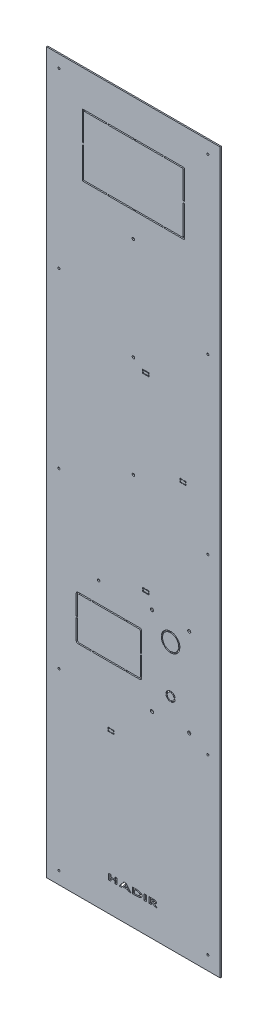
SolidWorks part; units mm, degrees
ref_plane "Front Plane" through (0, 0, 0) normal (0, 0, 1) x (1, 0, 0)
ref_plane "Top Plane" through (0, 0, 0) normal (0, 1, 0) x (1, 0, 0)
ref_plane "Right Plane" through (0, 0, 0) normal (1, 0, 0) x (0, 0, -1)
sketch "Sketch2" plane through (0, 0, 0) normal (0, 0, 1) x (1, 0, 0)
  line L0 (140, 680) -> (100, 680) construction
  line L5 (0, -480) -> (0, 680) construction
  line L6 (-140, 0) -> (140, 0) construction
  line L7 (100, 680) -> (100, 750.5127) construction
  line L8 (100, 750.5127) -> (100, -538.4561) construction
  line L9 (-140, 680) -> (-100, 680) construction
  line L10 (-100, 680) -> (-100, 750.5127) construction
  line L11 (-100, 750.5127) -> (-100, -538.4561) construction
  line L12 (-140, 680) -> (-140, 150) construction
  line L14 (-140, 680) -> (140, 680)
  line L15 (140, 680) -> (140, 580)
  line L17 (-140, -480) -> (140, -480)
  line L19 (140, -480) -> (140, 580)
  line L20 (-140, -480) -> (-140, 680)
  line L21 (-140, 150) -> (140, 150) construction
  line L22 (140, 150) -> (140, 110) construction
  line L23 (140, 110) -> (-140, 110) construction
  line L24 (0, 680) -> (0, 640) construction
  line L25 (-197.3636, 640) -> (197.5047, 640) construction
  line L26 (0, -480) -> (0, -440) construction
  line L27 (197.5047, -440) -> (-197.3636, -440) construction
  point P0 (0, 0)
  dimension "D1" = 1160
extrude "Boss-Extrude2" add sketch "Sketch2" along normal blind 2
sketch "Sketch3" plane through (0, 0, 0) normal (0, 0, 1) x (1, 0, 0)
  line L0 (120, 660) -> (120, 380.6) construction
  line L2 (-140, 660) -> (-120, 660) construction
  line L3 (120, 380.6) -> (-120, 380.6) construction
  line L4 (-120, 660) -> (-120, 680) construction
  line L5 (120, -457.6) -> (120, 101.2) construction
  line L6 (120, 101.2) -> (-120, 101.2) construction
  line L7 (-120, 680) -> (-120, 150) construction
  line L8 (-198.9172, 110) -> (186.996, 110) construction
  line L9 (-140, -480) -> (-100, -480) construction
  line L10 (60, -163) -> (90, -163) construction
  line L11 (0, 481.6) -> (0, 316.5) construction
  line L12 (-198.9172, 150) -> (186.996, 150) construction
  line L13 (0, 316.5) -> (0, 304.5) construction
  line L14 (186.996, 150) -> (186.996, 110) construction
  line L16 (60, -163) -> (30, -163) construction
  line L17 (-56.1, -21) -> (-56.1, -23) construction
  line L20 (-140, 680) -> (140, 680) construction
  line L23 (140, 660) -> (120, 660) construction
  line L24 (-56.1, 150) -> (-56.1, 110) construction
  line L25 (60, -21) -> (60, -36) construction
  line L26 (60, 0) -> (60, -21) construction
  line L27 (60, -21) -> (90, -21) construction
  line L28 (60, -127) -> (60, -163) construction
  line L29 (90, -163) -> (90, -21) construction
  line L30 (30, -163) -> (30, -21) construction
  line L31 (30, -21) -> (60, -21) construction
  line L127 (-140, 680) -> (-140, 640) construction
  line L132 (60, -36) -> (60, -38)
  line L137 (59.0006, -36.0333) -> (59.1224, -38.0297)
  line L222 (59.958, -51.042) -> (70.6066, -40.3934) construction
  line L223 (59.958, -51.042) -> (70.5575, -61.6415) construction
  line L224 (60, -51) -> (50.8076, -41.8076) construction
  line L225 (59.958, -51.042) -> (49.3934, -61.6066) construction
  line L230 (74.9337, -52.4092) -> (72.9425, -52.2213)
  line L231 (74.8066, -53.4011) -> (72.8324, -53.0809)
  line L232 (60, -66) -> (60, -64)
  line L233 (59.0005, -65.9671) -> (59.0005, -63.9615)
  line L250 (67.5, -127) -> (52.5, -127) construction
  line L251 (60, -127) -> (60, -119.5) construction
  line L252 (60, -119.5) -> (60, -121.5) construction
  line L253 (67.5, -127) -> (65.5, -127) construction
  line L254 (65.5, -127) -> (60, -127) construction
  line L255 (60, -127) -> (60, -132.5) construction
  line L256 (60, -127) -> (54.6967, -121.6967) construction
  line L257 (60, -127) -> (65.3033, -132.3033) construction
  line L258 (60, -127) -> (54.6967, -132.3033) construction
  line L259 (60, -127) -> (65.3033, -121.6967) construction
  line L260 (60.9806, -119.5644) -> (60.7191, -121.5472)
  line L261 (67.4356, -126.0194) -> (65.4528, -126.2809)
  line L262 (58.9874, -119.5687) -> (59.2574, -121.5504)
  line L263 (67.4356, -127.9806) -> (65.4528, -127.7191)
  line L264 (52.5644, -126.0194) -> (54.5472, -126.2809)
  line L265 (52.5644, -127.9806) -> (54.5472, -127.7191)
  line L266 (58.9874, -134.4313) -> (59.2574, -132.4496)
  line L267 (60.9806, -134.4356) -> (60.7191, -132.4528)
  line L268 (45.2633, -48.202) -> (47.2282, -48.5751)
  line L269 (45.1082, -49.202) -> (47.0937, -49.4417)
  line L270 (49.0202, -40.7803) -> (50.4841, -42.1429)
  line L271 (48.3636, -41.5346) -> (49.9151, -42.7966)
  line L272 (48.3636, -60.4655) -> (49.9151, -59.2034)
  line L273 (49.3934, -61.6066) -> (50.8076, -60.1924)
  line L274 (69.988, -62.191) -> (68.6563, -60.6989)
  line L275 (69.2202, -62.8317) -> (67.9908, -61.2541)
  line L276 (69.5589, -39.4403) -> (68.2844, -40.9816)
  line L277 (70.3079, -40.1029) -> (68.9335, -41.5558)
  line L295 (-32.1, -221.1) -> (-35.6, -221.1)
  line L304 (120, -457.6) -> (120, -178.2) construction
  line L305 (120, -178.2) -> (-120, -178.2) construction
  line L306 (100, 784.4571) -> (100, -643.8463) construction
  line L310 (30, -92) -> (13.48, -92) construction
  line L311 (-140, 640) -> (140, 640) construction
  line L314 (-140, -480) -> (-140, -440) construction
  line L315 (-140, -440) -> (140, -440) construction
  line L320 (-100, -480) -> (-100, 680) construction
  line L338 (-120, -480) -> (-120, -460) construction
  line L339 (-120, -460) -> (-140, -460) construction
  line L341 (120, -478.8) -> (120, -457.6) construction
  line L372 (120, -457.6) -> (140, -457.6) construction
  line L374 (140, 680) -> (140, 580) construction
  line L375 (120, 660) -> (120, 680) construction
  line L421 (0, 316.5) -> (0, 152.5) construction
  line L423 (0, 152.5) -> (0, 152.1) construction
  line L430 (0, 152.5) -> (80, 152.5) construction
  line L433 (0, 152.5) -> (0, -12.6) construction
  line L457 (0, -12.6) -> (0, 0) construction
  line L478 (0, 304.5) -> (20, 304.5) construction
  line L511 (-40.1, -221.1) -> (-40.1, -222.5)
  line L535 (-31.1, -220.1) -> (-35.6, -220.1)
  line L536 (-31.1, -220.1) -> (-31.1, -222.5)
  line L557 (24, 306.4) -> (24, 305)
  line L559 (25, 307.4) -> (20.5, 307.4)
  line L578 (80, 152.5) -> (80, 182.5) construction
  line L589 (-31.1, -225.9) -> (-35.6, -225.9)
  line L590 (-41.1, -220.1) -> (-41.1, -222.5)
  line L605 (0, 0) -> (20, 0) construction
  line L607 (24, 1.9) -> (24, 0.5)
  line L615 (-36.1, -224.9) -> (-36.1, -220.1) construction
  line L616 (-31.1, -223) -> (-41.1, -223) construction
  line L617 (-32.1, -224.9) -> (-35.6, -224.9)
  line L618 (-32.1, -221.1) -> (-32.1, -222.5)
  line L619 (-40.1, -223.5) -> (-40.1, -224.9)
  line L621 (-36.6, -224.9) -> (-40.1, -224.9)
  line L622 (-32.1, -223.5) -> (-32.1, -224.9)
  line L623 (-31.1, -223.5) -> (-32.1, -223.5)
  line L624 (-31.1, -222.5) -> (-32.1, -222.5)
  line L625 (-35.6, -220.1) -> (-35.6, -221.1)
  line L626 (-36.6, -220.1) -> (-36.6, -221.1)
  line L627 (-35.6, -224.9) -> (-35.6, -225.9)
  line L628 (-36.6, -224.9) -> (-36.6, -225.9)
  line L629 (-40.1, -222.5) -> (-41.1, -222.5)
  line L630 (-40.1, -223.5) -> (-41.1, -223.5)
  line L631 (-36.6, -220.1) -> (-41.1, -220.1)
  line L632 (-31.1, -220.1) -> (-41.1, -220.1) construction
  line L633 (-36.6, -221.1) -> (-40.1, -221.1)
  line L634 (-32.1, -221.1) -> (-40.1, -221.1) construction
  line L635 (-32.1, -224.9) -> (-40.1, -224.9) construction
  line L636 (-36.6, -225.9) -> (-41.1, -225.9)
  line L637 (-31.1, -225.9) -> (-41.1, -225.9) construction
  line L638 (-31.1, -223.5) -> (-31.1, -225.9)
  line L639 (-31.1, -220.1) -> (-31.1, -225.9) construction
  line L640 (-32.1, -221.1) -> (-32.1, -224.9) construction
  line L641 (-40.1, -221.1) -> (-40.1, -224.9) construction
  line L642 (-41.1, -223.5) -> (-41.1, -225.9)
  line L643 (-41.1, -220.1) -> (-41.1, -225.9) construction
  line L709 (-140, 680) -> (-140, -480) construction
  line L724 (81.2, 622.2) -> (50.0052, 622.2)
  line L726 (82.2, 621.2) -> (82.2, 575.26)
  line L729 (81.2, 521.6) -> (50.0052, 521.6)
  line L730 (-82.2, 522.6) -> (-82.2, 572.28)
  line L732 (79.2, 620.2) -> (50.0052, 620.2)
  line L734 (-80.2, 524.6) -> (-80.2, 572.28)
  line L741 (79.2, 523.6) -> (50.0052, 523.6)
  line L743 (80.2, 619.2) -> (80.2, 575.26)
  line L746 (-0.015, 523.6) -> (-41.1248, 523.6)
  line L747 (48.0052, 620.2) -> (1.985, 620.2)
  line L748 (1.985, 622.2) -> (1.985, 620.2)
  line L749 (-0.015, 622.2) -> (-0.015, 620.2)
  line L750 (1.985, 523.6) -> (1.985, 521.6)
  line L751 (-0.015, 523.6) -> (-0.015, 521.6)
  line L752 (-41.1248, 622.2) -> (-41.1248, 620.2)
  line L753 (-41.1248, 523.6) -> (-41.1248, 521.6)
  line L754 (-0.015, 620.2) -> (-41.1248, 620.2)
  line L755 (-43.1248, 622.2) -> (-43.1248, 620.2)
  line L756 (-43.1248, 523.6) -> (-43.1248, 521.6)
  line L757 (50.0052, 622.2) -> (50.0052, 620.2)
  line L758 (50.0052, 523.6) -> (50.0052, 521.6)
  line L759 (80.2, 572.28) -> (80.2, 524.6)
  line L760 (48.0052, 622.2) -> (48.0052, 620.2)
  line L761 (48.0052, 523.6) -> (48.0052, 521.6)
  line L762 (140, 680) -> (-140, 680) construction
  line L763 (82.2, 572.28) -> (80.2, 572.28)
  line L764 (140, -480) -> (140, 680) construction
  line L765 (82.2, 575.26) -> (80.2, 575.26)
  line L766 (-80.2, 575.26) -> (-82.2, 575.26)
  line L767 (-80.2, 572.28) -> (-82.2, 572.28)
  line L768 (-82.2, 575.26) -> (-82.2, 621.2)
  line L769 (-82.2, 521.6) -> (-82.2, 622.2) construction
  line L770 (-80.2, 575.26) -> (-80.2, 619.2)
  line L771 (-80.2, 523.6) -> (-80.2, 620.2) construction
  line L772 (-43.1248, 622.2) -> (-81.2, 622.2)
  line L773 (82.2, 622.2) -> (-82.2, 622.2) construction
  line L774 (-43.1248, 620.2) -> (-79.2, 620.2)
  line L775 (80.2, 620.2) -> (-80.2, 620.2) construction
  line L776 (-43.1248, 523.6) -> (-79.2, 523.6)
  line L777 (80.2, 523.6) -> (-80.2, 523.6) construction
  line L778 (-43.1248, 521.6) -> (-81.2, 521.6)
  line L779 (82.2, 521.6) -> (-82.2, 521.6) construction
  line L780 (-0.015, 622.2) -> (-41.1248, 622.2)
  line L781 (-0.015, 521.6) -> (-41.1248, 521.6)
  line L782 (48.0052, 622.2) -> (1.985, 622.2)
  line L783 (48.0052, 523.6) -> (1.985, 523.6)
  line L784 (48.0052, 521.6) -> (1.985, 521.6)
  line L785 (82.2, 572.28) -> (82.2, 522.6)
  line L786 (82.2, 622.2) -> (82.2, 521.6) construction
  line L787 (80.2, 620.2) -> (80.2, 523.6) construction
  line L794 (-11.5164, -128) -> (10.48, -128)
  line L795 (-11.5164, -126) -> (8.48, -126)
  line L796 (13.48, -93) -> (13.48, -125)
  line L797 (11.48, -93) -> (11.48, -123)
  line L798 (-68, -126) -> (-87.12, -126)
  line L799 (-68, -126) -> (-68, -128)
  line L800 (84, 184.4) -> (84, 183)
  line L801 (85, 185.4) -> (80.5, 185.4)
  line L802 (-39.32, -56) -> (-38.32, -56) construction
  line L803 (-39.32, -56) -> (-40.32, -56) construction
  line L804 (-11.5164, -56) -> (-11.5164, -58)
  line L805 (-11.5164, -126) -> (-11.5164, -128)
  line L807 (-13.5164, -56) -> (-13.5164, -58)
  line L809 (-90.12, -93) -> (-92.12, -93)
  line L810 (-0.015, 521.6) -> (0, 481.6) construction
  line L811 (-90.12, -91) -> (-92.12, -91)
  line L814 (13.48, -93) -> (11.48, -93)
  line L815 (13.48, -91) -> (11.48, -91)
  line L816 (-13.5164, -126) -> (-13.5164, -128)
  line L817 (-68, -56) -> (-68, -58)
  line L820 (-66, -56) -> (-66, -58)
  line L821 (-66, -126) -> (-66, -128)
  line L822 (-66, -56) -> (-13.5164, -56)
  line L823 (-66, -58) -> (-13.5164, -58)
  line L827 (-13.5164, -126) -> (-66, -126)
  line L828 (-13.5164, -128) -> (-66, -128)
  line L843 (25, 307.4) -> (25, 305)
  line L845 (25, 301.6) -> (20.5, 301.6)
  line L846 (15, 307.4) -> (15, 305)
  line L848 (20, 301.6) -> (20, 307.4) construction
  line L849 (25, 304.5) -> (15, 304.5) construction
  line L851 (24, 302.6) -> (20.5, 302.6)
  line L852 (16, 306.4) -> (16, 305)
  line L854 (24, 306.4) -> (20.5, 306.4)
  line L859 (25, 2.9) -> (20.5, 2.9)
  line L870 (80, 179.6) -> (80, 185.4) construction
  line L872 (85, 182.5) -> (75.5701, 182.5) construction
  line L878 (19.5, 302.6) -> (16, 302.6)
  line L879 (24, 302.6) -> (16, 302.6) construction
  line L889 (25, 2.9) -> (25, 0.5)
  line L891 (25, -2.9) -> (20.5, -2.9)
  line L893 (15, 2.9) -> (15, 0.5)
  line L895 (20, -2.9) -> (20, 2.9) construction
  line L897 (25, 0) -> (15, 0) construction
  line L899 (24, -1.9) -> (20.5, -1.9)
  line L901 (16, 1.9) -> (16, 0.5)
  line L902 (19.5, 306.4) -> (16, 306.4)
  line L904 (25, 305) -> (24, 305)
  line L905 (25, 304) -> (24, 304)
  line L906 (15, 305) -> (16, 305)
  line L907 (15, 304) -> (16, 304)
  line L908 (20.5, 307.4) -> (20.5, 306.4)
  line L909 (19.5, 307.4) -> (19.5, 306.4)
  line L910 (20.5, 302.6) -> (20.5, 301.6)
  line L911 (19.5, 302.6) -> (19.5, 301.6)
  line L912 (25, 304) -> (25, 301.6)
  line L913 (25, 307.4) -> (25, 301.6) construction
  line L914 (24, 304) -> (24, 302.6)
  line L915 (24, 306.4) -> (24, 302.6) construction
  line L916 (24, 306.4) -> (16, 306.4) construction
  line L917 (19.5, 307.4) -> (15, 307.4)
  line L918 (25, 307.4) -> (15, 307.4) construction
  line L919 (19.5, 301.6) -> (15, 301.6)
  line L920 (25, 301.6) -> (15, 301.6) construction
  line L921 (16, 304) -> (16, 302.6)
  line L922 (16, 306.4) -> (16, 302.6) construction
  line L923 (15, 304) -> (15, 301.6)
  line L924 (15, 307.4) -> (15, 301.6) construction
  line L925 (24, 1.9) -> (20.5, 1.9)
  line L927 (85, 185.4) -> (85, 183)
  line L937 (85, 179.6) -> (80.5, 179.6)
  line L939 (75, 185.4) -> (75, 183)
  line L941 (80, 179.6) -> (80, 185.4) construction
  line L942 (85, 182.5) -> (75, 182.5) construction
  line L944 (84, 180.6) -> (80.5, 180.6)
  line L946 (76, 184.4) -> (76, 183)
  line L948 (84, 184.4) -> (80.5, 184.4)
  line L949 (24, -0.5) -> (24, -1.9)
  line L950 (19.5, -2.9) -> (15, -2.9)
  line L951 (25, -2.9) -> (15, -2.9) construction
  line L953 (25, -0.5) -> (24, -0.5)
  line L954 (25, 0.5) -> (24, 0.5)
  line L955 (20.5, 2.9) -> (20.5, 1.9)
  line L956 (19.5, 2.9) -> (19.5, 1.9)
  line L957 (20.5, -1.9) -> (20.5, -2.9)
  line L958 (19.5, -1.9) -> (19.5, -2.9)
  line L959 (16, 0.5) -> (15, 0.5)
  line L960 (16, -0.5) -> (15, -0.5)
  line L961 (19.5, 2.9) -> (15, 2.9)
  line L962 (25, 2.9) -> (15, 2.9) construction
  line L963 (19.5, 1.9) -> (16, 1.9)
  line L964 (24, 1.9) -> (16, 1.9) construction
  line L965 (24, 1.9) -> (24, -1.9) construction
  line L966 (25, -0.5) -> (25, -2.9)
  line L967 (25, 2.9) -> (25, -2.9) construction
  line L968 (19.5, -1.9) -> (16, -1.9)
  line L969 (24, -1.9) -> (16, -1.9) construction
  line L970 (15, -0.5) -> (15, -2.9)
  line L971 (15, 2.9) -> (15, -2.9) construction
  line L972 (16, -0.5) -> (16, -1.9)
  line L973 (16, 1.9) -> (16, -1.9) construction
  line L987 (-68, -56) -> (-89.12, -56)
  line L988 (-92.12, -91) -> (-92.12, -59)
  line L989 (-90.12, -91) -> (-90.12, -61)
  line L990 (-68, -58) -> (-87.12, -58)
  line L991 (-92.12, -93) -> (-92.12, -125)
  line L992 (-90.12, -93) -> (-90.12, -123)
  line L993 (-68, -128) -> (-89.12, -128)
  line L994 (79.5, 180.6) -> (76, 180.6)
  line L995 (13.48, -91) -> (13.48, -59)
  line L996 (11.48, -91) -> (11.48, -61)
  line L997 (-11.5164, -56) -> (10.48, -56)
  line L998 (-11.5164, -58) -> (8.48, -58)
  line L999 (76, 182.04) -> (76, 180.6)
  line L1000 (80.5, 185.4) -> (80.5, 184.4)
  line L1001 (79.5, 185.4) -> (79.5, 184.4)
  line L1002 (80.5, 180.6) -> (80.5, 179.6)
  line L1003 (79.5, 180.6) -> (79.5, 179.6)
  line L1004 (85, 182.04) -> (85, 179.6)
  line L1005 (76, 182.04) -> (75, 182.04)
  line L1007 (75, 183) -> (76, 183)
  line L1008 (84, 183) -> (85, 183)
  line L1009 (85, 182.04) -> (84, 182.04)
  line L1010 (79.5, 185.4) -> (75, 185.4)
  line L1011 (85, 185.4) -> (75, 185.4) construction
  line L1012 (79.5, 184.4) -> (76, 184.4)
  line L1013 (84, 184.4) -> (76, 184.4) construction
  line L1014 (84, 180.6) -> (76, 180.6) construction
  line L1015 (79.5, 179.6) -> (75, 179.6)
  line L1016 (85, 179.6) -> (75, 179.6) construction
  line L1017 (75, 182.04) -> (75, 179.6)
  line L1018 (75, 185.4) -> (75, 179.6) construction
  line L1019 (76, 184.4) -> (76, 180.6) construction
  line L1020 (85, 185.4) -> (85, 179.6) construction
  line L1021 (84, 182.04) -> (84, 180.6)
  line L1022 (84, 184.4) -> (84, 180.6) construction
  circle A27 centre (-56.1, -23) radius 2
  arc A80 (60.9806, -119.5644) -> (67.4356, -126.0194) centre (60, -127) cw
  arc A96 (67.4356, -127.9806) -> (60.9806, -134.4356) centre (60, -127) cw
  arc A99 (58.9874, -134.4313) -> (52.5644, -127.9806) centre (60, -127) cw
  arc A109 (58.9874, -119.5687) -> (52.5644, -126.0194) centre (60, -127) ccw
  arc A110 (60.7191, -121.5472) -> (65.4528, -126.2809) centre (60, -127) cw
  arc A111 (65.4528, -127.7191) -> (60.7191, -132.4528) centre (60, -127) cw
  arc A112 (59.2574, -132.4496) -> (54.5472, -127.7191) centre (60, -127) cw
  arc A113 (54.5472, -126.2809) -> (59.2574, -121.5504) centre (60, -127) cw
  arc A121 (70.3079, -40.1029) -> (74.9337, -52.4092) centre (60, -51) cw
  circle A122 centre (-120, -460) radius 1.65
  arc A123 (68.9335, -41.5558) -> (72.9425, -52.2213) centre (60, -51) cw
  arc A124 (72.8324, -53.0809) -> (68.6563, -60.6989) centre (60, -51) cw
  arc A125 (74.8066, -53.4011) -> (69.988, -62.191) centre (60, -51) cw
  arc A126 (69.2202, -62.8317) -> (60, -66) centre (60, -51) cw
  arc A127 (67.9908, -61.2541) -> (60, -64) centre (60, -51) cw
  arc A128 (59.0005, -63.9615) -> (50.8076, -60.1924) centre (60, -51) cw
  arc A129 (59.0005, -65.9671) -> (49.3934, -61.6066) centre (60.0005, -51.0005) cw
  arc A130 (49.9151, -59.2034) -> (47.0937, -49.4417) centre (60, -51) cw
  arc A131 (48.3636, -60.4655) -> (45.1082, -49.202) centre (60, -51) cw
  arc A132 (47.2282, -48.5751) -> (49.9151, -42.7966) centre (60, -51) cw
  arc A133 (45.2633, -48.202) -> (48.3636, -41.5346) centre (60, -51) cw
  arc A134 (50.4841, -42.1429) -> (59.1224, -38.0297) centre (60, -51) cw
  arc A135 (59.0006, -36.0333) -> (49.0202, -40.7803) centre (60, -51) ccw
  arc A136 (60, -36) -> (69.5589, -39.4403) centre (60, -51) cw
  arc A137 (60, -38) -> (68.2844, -40.9816) centre (60, -51) cw
  circle A138 centre (120, -457.6) radius 1.65
  circle A140 centre (90, -21) radius 2.5
  circle A141 centre (90, -163) radius 2.5
  circle A142 centre (30, -163) radius 2.5
  circle A143 centre (30, -21) radius 2.5
  circle A144 centre (-120, 660) radius 1.65
  circle A145 centre (120, 660) radius 1.65
  circle A146 centre (-120, 380.6) radius 1.65
  circle A147 centre (120, 380.6) radius 1.65
  circle A152 centre (120, -178.2) radius 1.65
  circle A153 centre (-120, -178.2) radius 1.65
  circle A154 centre (120, 101.2) radius 1.65
  circle A155 centre (-120, 101.2) radius 1.65
  arc A158 (-81.2, 521.6) -> (-82.2, 522.6) centre (-81.2, 522.6) cw
  arc A159 (-80.2, 524.6) -> (-79.2, 523.6) centre (-79.2, 524.6) ccw
  arc A160 (-81.2, 622.2) -> (-82.2, 621.2) centre (-81.2, 621.2) ccw
  arc A161 (-79.2, 620.2) -> (-80.2, 619.2) centre (-79.2, 619.2) ccw
  arc A162 (82.2, 522.6) -> (81.2, 521.6) centre (81.2, 522.6) cw
  arc A163 (79.2, 523.6) -> (80.2, 524.6) centre (79.2, 524.6) ccw
  arc A164 (79.2, 620.2) -> (80.2, 619.2) centre (79.2, 619.2) cw
  arc A165 (81.2, 622.2) -> (82.2, 621.2) centre (81.2, 621.2) cw
  circle A174 centre (0, 481.6) radius 2
  circle A175 centre (0, 316.5) radius 2
  circle A177 centre (0, 152.5) radius 2
  arc A186 (-92.12, -125) -> (-89.12, -128) centre (-89.12, -125) ccw
  arc A187 (-90.12, -123) -> (-87.12, -126) centre (-87.12, -123) ccw
  arc A188 (-89.12, -56) -> (-92.12, -59) centre (-89.12, -59) ccw
  arc A189 (-90.12, -61) -> (-87.12, -58) centre (-87.12, -61) cw
  arc A190 (10.48, -128) -> (13.48, -125) centre (10.48, -125) ccw
  arc A191 (8.48, -126) -> (11.48, -123) centre (8.48, -123) ccw
  arc A192 (11.48, -61) -> (8.48, -58) centre (8.48, -61) ccw
  arc A193 (13.48, -59) -> (10.48, -56) centre (10.48, -59) ccw
  point P56 (0, 623.18)
  point P126 (-36.1, -223)
  point P186 (13.48, -92)
  point P251 (60, -51)
  point P323 (0, 623.18)
  point P411 (-82.2, 598.23)
  dimension "D8" = 3
  dimension "D9" = 530
  dimension "D10" = 3.3
  dimension "D11" = 105.6
  dimension "D12" = 165.1
  dimension "D13" = 2
  dimension "D14" = 5
  dimension "D15" = 15
  dimension "D16" = 21
  dimension "D17" = 5
  dimension "D18" = 72
  dimension "D19" = 5
  dimension "D20" = 279.4
  dimension "D21" = 4
  dimension "D24" = 4
  dimension "D25" = 5.8
  dimension "D37" = 279.4
  dimension "D44" = 10
  dimension "D39" = 279.4
  dimension "D40" = 5.8
  dimension "D49" = 164
  dimension "D53" = 5.8
  dimension "D57" = 10
  dimension "D60" = 1
  dimension "D61" = 100.6
  dimension "D62" = 1
  dimension "D54" = 45
  dimension "D56" = 45
  dimension "D63" = 164.4
  dimension "D66" = 57.8
  dimension "D67" = 57.8
  dimension "D55" = 1
  dimension "D48" = 1
  dimension "D68" = 1
  dimension "D69" = 57.8
  dimension "D30" = 3.3
  dimension "D31" = 3.3
  dimension "D46" = 1
  dimension "D36" = 5
  dimension "D26" = 3.3
  dimension "D27" = 3.3
  dimension "D28" = 3.3
  dimension "D22" = 4
  dimension "D23" = 3.3
  dimension "D32" = 3.3
  dimension "D33" = 3.3
  dimension "D41" = 3.3
  dimension "D58" = 2
  dimension "D64" = 4
  dimension "D43" = 5.8
  dimension "D29" = 279.4
  dimension "D34" = 40
  dimension "D35" = 10
  dimension "D38" = 1
  dimension "D42" = 10
  dimension "D45" = 1
  dimension "D47" = 40
  dimension "D50" = 1
  dimension "D51" = 165.1
  dimension "D52" = 1
  dimension "D70" = 1
  dimension "D71" = 1
extrude "Cut-Extrude8" cut sketch "Sketch3" along normal blind 2
sketch "Sketch4" plane through (0, 0, 0) normal (0, 0, 1) x (1, 0, 0)
  line L0 (-121.7889, -433.1206) -> (118.2111, -433.1206) construction
  text T0 "<b>HADIR</b>" font "Century Gothic" height in points 36
extrude "Cut-Extrude9" cut sketch "Sketch4" along normal blind 2
